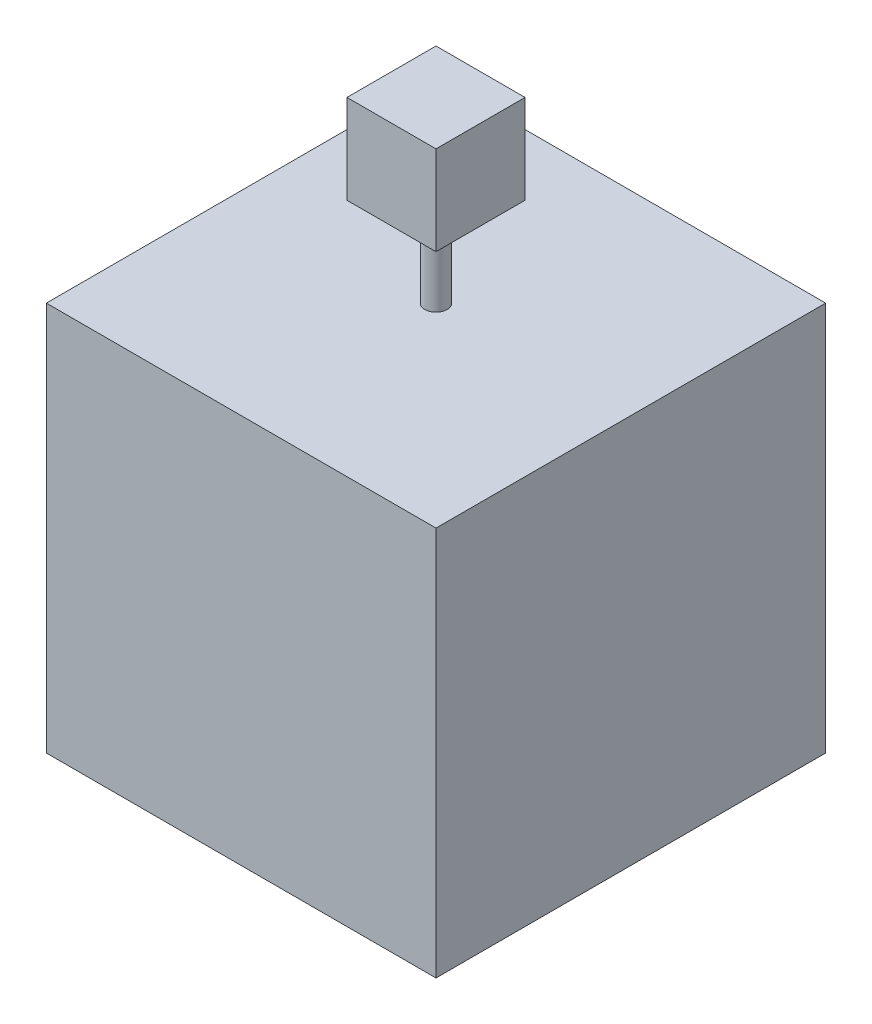
SolidWorks part; units mm, degrees
ref_plane "Plan de face" through (0, 0, 0) normal (0, 0, 1) x (1, 0, 0)
ref_plane "Plan de dessus" through (0, 0, 0) normal (0, 1, 0) x (1, 0, 0)
ref_plane "Plan de droite" through (0, 0, 0) normal (1, 0, 0) x (0, 0, -1)
sketch "Esquisse1" plane through (0, 0, 0) normal (0, 1, 0) x (1, 0, 0)
  line L1 (0, 0) -> (350, 0)
  line L2 (0, 0) -> (0, 350)
  line L3 (0, 350) -> (350, 350)
  line L4 (350, 0) -> (350, 350)
  dimension "D1" = 350
extrude "Extrusion1" add sketch "Esquisse1" along normal blind 350
sketch "Esquisse2" plane through (0, 350, 0) normal (0, 1, 0) x (1, 0, 0)
  line L0 (175, 350) -> (175, 0) construction
  line L1 (350, 350) -> (0, 350) construction
  line L2 (0, 0) -> (350, 0) construction
  line L3 (0, 175) -> (350, 175) construction
  line L4 (0, 350) -> (0, 0) construction
  line L5 (350, 0) -> (350, 350) construction
  circle A0 centre (175, 175) radius 10
  dimension "D1" = 20
extrude "Extrusion2" add sketch "Esquisse2" along normal blind 80
sketch "Esquisse3" plane through (0, 430, 0) normal (0, 1, 0) x (1, 0, 0)
  line L0 (175, 175) -> (175, 215) construction
  line L1 (175, 175) -> (215, 175) construction
  line L3 (135, 215) -> (215, 215)
  line L4 (135, 215) -> (135, 135)
  line L5 (135, 135) -> (215, 135)
  line L6 (215, 215) -> (215, 135)
  dimension "D1" = 80
extrude "Extrusion3" add sketch "Esquisse3" along normal blind 80
